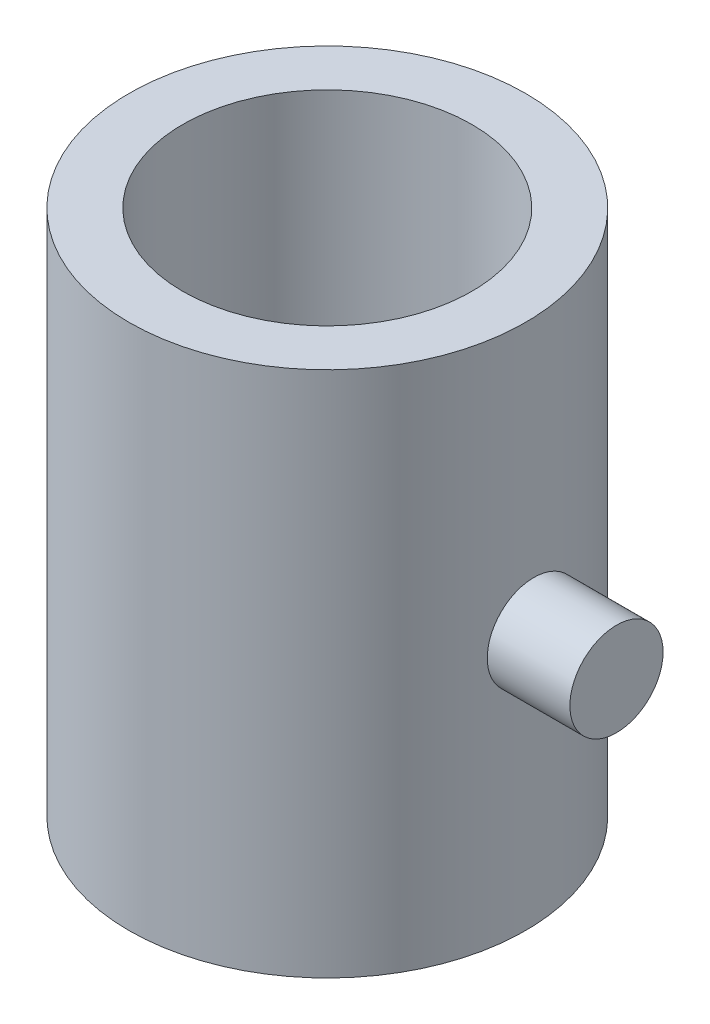
SolidWorks part; units mm, degrees
ref_plane "Front Plane" through (0, 0, 0) normal (0, 0, 1) x (1, 0, 0)
ref_plane "Top Plane" through (0, 0, 0) normal (0, 1, 0) x (1, 0, 0)
ref_plane "Right Plane" through (0, 0, 0) normal (1, 0, 0) x (0, 0, -1)
sketch "Sketch1" plane through (0, 0, 0) normal (0, 1, 0) x (1, 0, 0)
  circle A0 centre (0, 0) radius 3.5
  circle A1 centre (0, 0) radius 4.8
  dimension "D1" = 7
  dimension "D2" = 9.6
extrude "Boss-Extrude1" add sketch "Sketch1" along normal mid plane 12.75
sketch "Sketch2" plane through (0, 0, 0) normal (1, 0, 0) x (0, 0, -1)
  circle A0 centre (0, 0) radius 1.1281
extrude "Boss-Extrude2" add sketch "Sketch2" along normal blind 2 from offset 5
